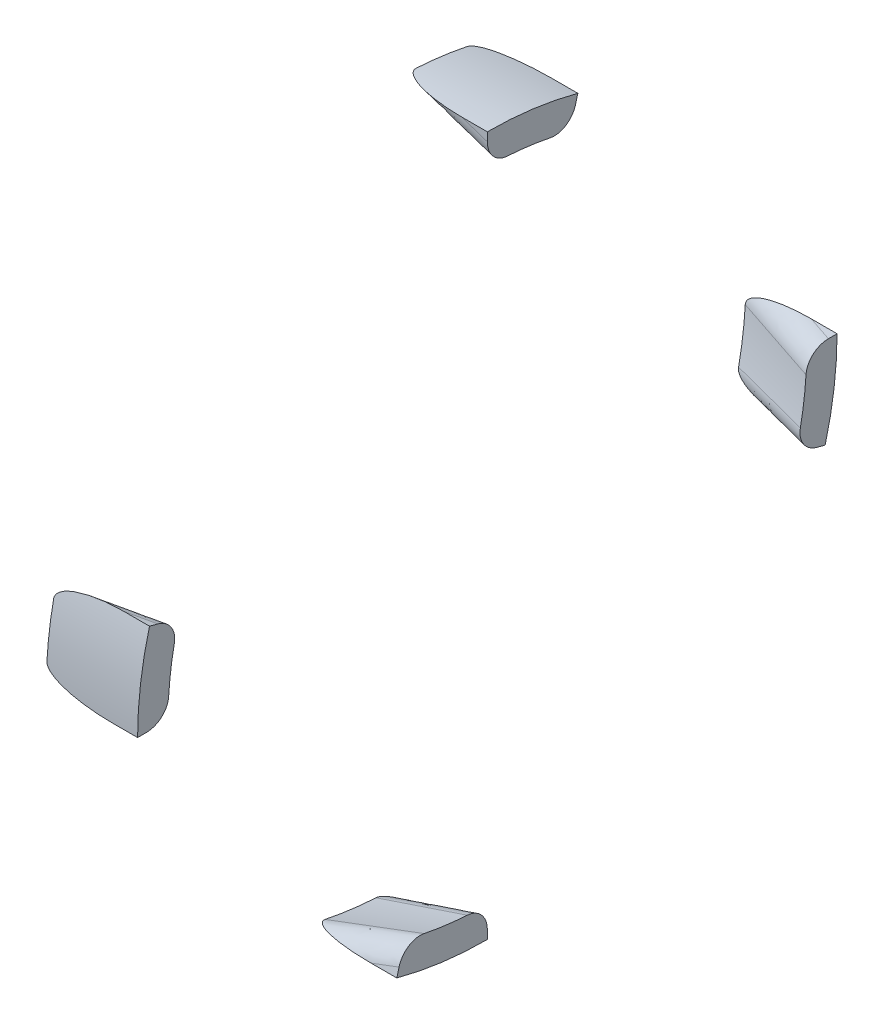
SolidWorks part; units mm, degrees
material "Hexcel AS4C (3000 Filaments)"
ref_plane "Front Plane" through (0, 0, 0) normal (0, 0, 1) x (1, 0, 0)
ref_plane "Top Plane" through (0, 0, 0) normal (0, 1, 0) x (1, 0, 0)
ref_plane "Right Plane" through (0, 0, 0) normal (1, 0, 0) x (0, 0, -1)
sketch "Sketch1" plane through (0, 0, 0) normal (0, 0, 1) x (1, 0, 0)
  line L0 (0, 0) -> (-38.1, 0)
  line L1 (-38.1, 0) -> (0, -12.7)
  line L2 (0, -12.7) -> (0, 0)
  line L3 (0, -12.7) -> (0, -146.05) construction
  line L4 (0, -146.05) -> (-86.1056, -146.05) construction
  dimension "D1" = 12.7
  dimension "D2" = 38.1
  dimension "D3" = 133.35
revolve "Revolve1" add sketch "Sketch1" angle 15 about L4
sketch3d "3DSketch1"
  line L0 (0, -12.7, 0) -> (0, -146.05, 0) construction
  line L1 (0, -146.05, 0) -> (-94.3391, -146.05, 0) construction
  dimension "D1" = 133.35
pattern_circular "CirPattern1" count 4 every 90 about axis through (0, -146.05, 0) along (-1, 0, 0) of bodies 101
fillet "Fillet1" radius 8.89 2 edges at (-19.05, -11.1102, -36.157) (-19.05, -6.35, 0)
fillet "Fillet2" radius 8.89 2 edges at (-19.05, -109.893, 134.9398) (-19.05, -146.05, 139.7)
fillet "Fillet3" radius 8.89 2 edges at (-19.05, -280.9898, 36.157) (-19.05, -285.75, 0)
fillet "Fillet4" radius 8.89 2 edges at (-19.05, -182.207, -134.9398) (-19.05, -146.05, -139.7)
